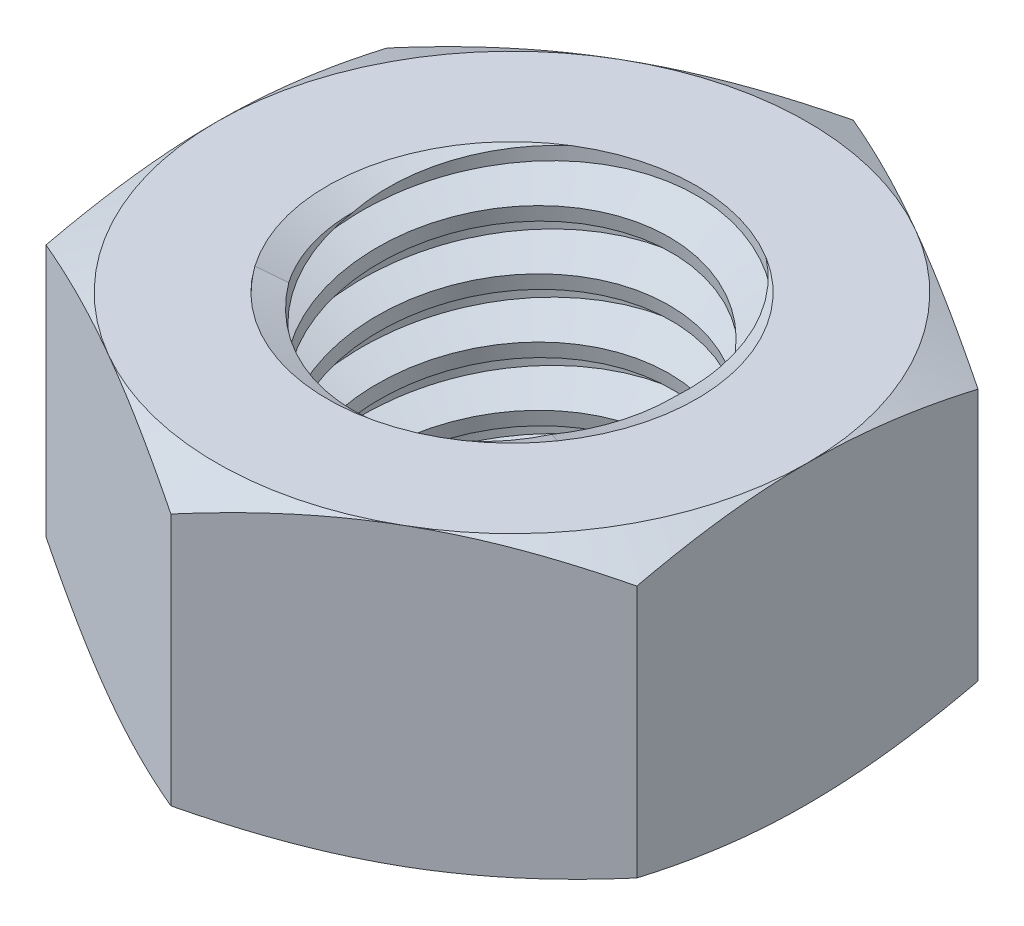
SolidWorks part; units mm, degrees
ref_plane "Front" through (0, 0, 0) normal (0, 0, 1) x (1, 0, 0)
ref_plane "Top" through (0, 0, 0) normal (0, 1, 0) x (1, 0, 0)
ref_plane "Right" through (0, 0, 0) normal (1, 0, 0) x (0, 0, -1)
sketch "Sketch1" plane through (0, 0, 0) normal (0, 1, 0) x (1, 0, 0)
  line L1 (0, 4.6188) -> (-4, 2.3094)
  line L2 (-4, 2.3094) -> (-4, -2.3094)
  line L3 (-4, -2.3094) -> (0, -4.6188)
  line L4 (0, -4.6188) -> (4, -2.3094)
  line L5 (4, -2.3094) -> (4, 2.3094)
  line L6 (4, 2.3094) -> (0, 4.6188)
  circle A0 centre (0, 0) radius 4 construction
  dimension "Hex Flats" = 8
extrude "Extrude1" add sketch "Sketch1" along normal mid plane 4
sketch "Sketch2" plane through (0, 0, 0) normal (1, 0, 0) x (0, 0, -1)
  line L0 (-2.5, -2) -> (-2.5, 2) construction
  line L1 (0, -2) -> (2.5, -2)
  line L2 (0, -2) -> (0, 2)
  line L3 (0, 2) -> (2.5, 2)
  line L4 (2.5, -2) -> (2.5, 2)
  line L5 (-2.3094, 2) -> (2.3094, 2) construction
  line L6 (-2.3094, -2) -> (2.3094, -2) construction
  line L7 (0, -4.5) -> (0, -2) construction
  dimension "Thread Dia" = 5
revolve "Revolve1" add sketch "Sketch2" angle 360 about L7
sketch "Sketch3" plane through (0, 0, 0) normal (1, 0, 0) x (0, 0, -1)
  line L0 (2.5, 2) -> (-2.5, 2) construction
  line L1 (-2.5, 2) -> (-2.5, 1.2) construction
  line L2 (-2.5, 1.2) -> (2.5, 2) construction
  line L3 (2.5, 2) -> (2.5158, 1.9013) construction
  line L4 (2.5158, 1.9013) -> (2.6264, 1.21)
  line L5 (2.6264, 1.21) -> (2.1593, 1.3885)
  line L6 (2.1593, 1.3885) -> (2.1277, 1.586)
  line L7 (2.1277, 1.586) -> (2.5158, 1.9013)
  line L8 (2.1435, 1.4872) -> (2.5711, 1.5557) construction
  line L9 (2.5, 2) -> (2.5, 1.5443) construction
  line L10 (2.5, 1.5443) -> (-2.5, 0.7443) construction
  line L11 (-2.5, 0.7443) -> (-2.5, 1.2) construction
  line L12 (-0.1369, 2) -> (0.1369, 0.2886) construction
  line L13 (-2.5, -2) -> (-2.5, 2) construction
  line L14 (0, 2) -> (2.5, 2) construction
  line L15 (2.5, -2) -> (2.5, 2) construction
  line L16 (0, 0) -> (0, 2) construction
  line L17 (-2.5158, 1.9013) -> (-2.6264, 1.21) construction
  line L18 (-2.1277, 1.586) -> (-2.5158, 1.9013) construction
  line L19 (-2.1593, 1.3885) -> (-2.1277, 1.586) construction
  line L20 (-2.6264, 1.21) -> (-2.1593, 1.3885) construction
  line L21 (0.1369, 2) -> (-0.1369, 0.2886) construction
  point P13 (0, 1.1443)
  dimension "D1" = 0.1
  dimension "D2" = 0.2
  dimension "Thread Pitch" = 0.8
  dimension "D4" = 60
  dimension "D5" = 0.8
revolve "Cut-Revolve1" cut sketch "Sketch3" angle 360 about L12
pattern_linear "LPattern1" count 5 spacing 0.8 along (0, -1, 0) count 2 spacing 0.8 along (0, 1, 0) of "Cut-Revolve1"
sketch "Sketch4" plane through (0, 0, 0) normal (1, 0, 0) x (0, 0, -1)
  line L0 (0, 2) -> (2.5, 2)
  line L1 (2.5, 2) -> (2.1277, 1.8264)
  line L2 (2.1277, 1.8264) -> (2.1277, -1.8264)
  line L3 (2.1277, -1.8264) -> (2.5, -2)
  line L4 (2.5, -2) -> (0, -2)
  line L5 (0, -2) -> (0, 2)
  line L6 (2.5, -2) -> (2.5, 2) construction
  line L7 (0, 2) -> (2.5, 2) construction
  line L8 (0, -2) -> (2.5, -2) construction
  line L9 (0, -2) -> (0, 2) construction
  line L10 (0, 2) -> (0, 2.4108) construction
  dimension "D1" = 25
revolve "Cut-Revolve2" cut sketch "Sketch4" angle 360 about L10
combine bodies "Combine1" operation type subtract main body 112 bodies to subtract 111
sketch "Sketch5" plane through (0, 0, 0) normal (1, 0, 0) x (0, 0, -1)
  line L0 (0, -2) -> (4, -2)
  line L1 (4, -2) -> (4.6188, -1.7114)
  line L2 (4.6188, -1.7114) -> (4.6188, 1.7114)
  line L3 (4.6188, 1.7114) -> (4, 2)
  line L4 (0, 2) -> (0, 3.27)
  line L5 (0, 3.27) -> (5.8888, 3.27)
  line L6 (5.8888, 3.27) -> (5.8888, -3.27)
  line L7 (5.8888, -3.27) -> (0, -3.27)
  line L8 (0, -3.27) -> (0, -2)
  line L9 (4, 2) -> (4, -2) construction
  line L11 (0, -2) -> (2.5, -2) construction
  line L12 (4, 2) -> (0, 2)
  line L13 (4.6188, 0) -> (5.8888, 0) construction
  line L14 (4.6188, 2) -> (4.6188, -2) construction
  line L15 (0, -2) -> (0, 2) construction
  line L17 (0, 0) -> (4, 0) construction
  line L22 (0, 2) -> (2.5, 2) construction
  dimension "D1" = 25
  dimension "D2" = 1.27
  dimension "D3" = 4
revolve "Cut-Revolve3" cut sketch "Sketch5" angle 360 about L15
equation "\"D1@Sketch3\"=\"Thread Pitch@Sketch3\"/8"
equation "\"D2@Sketch3\"=\"Thread Pitch@Sketch3\"/4"
equation "\"D5@Sketch3\"=\"Thread Pitch@Sketch3\""
equation "\"D4@LPattern1\"=\"Thread Pitch@Sketch3\""
equation "\"D3@LPattern1\"=\"Thread Pitch@Sketch3\""
equation "\"D1@LPattern1\"=\"Height@Extrude1\"/\"Thread Pitch@Sketch3\""
